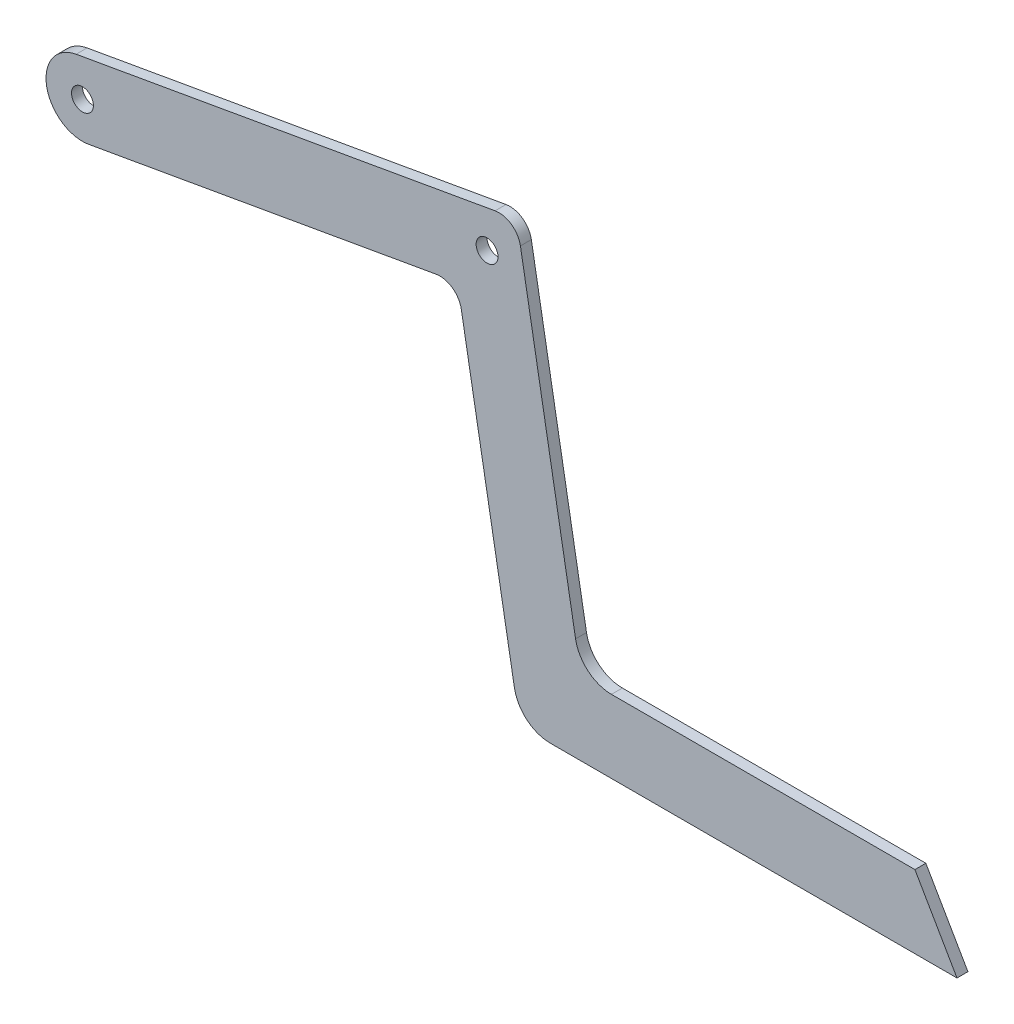
SolidWorks part; units mm, degrees
ref_plane "Front Plane" through (0, 0, 0) normal (0, 0, 1) x (1, 0, 0)
ref_plane "Top Plane" through (0, 0, 0) normal (0, 1, 0) x (1, 0, 0)
ref_plane "Right Plane" through (0, 0, 0) normal (1, 0, 0) x (0, 0, -1)
sketch "Sketch1" plane through (0, 0, 0) normal (0, 0, 1) x (1, 0, 0)
  line L0 (4.1955, 0) -> (60, 0)
  line L5 (60, 0) -> (54.2265, 10)
  line L6 (54.2265, 10) -> (12.5865, 10)
  line L8 (7.6625, 14.1318) -> (0.0956, 57.0456)
  line L9 (-60, 44.4182) -> (30.0016, 60.288) construction
  line L10 (-3.3798, 59.4791) -> (-60.8682, 49.3423)
  line L11 (-11.4914, 47.8945) -> (-59.1318, 39.4942)
  line L12 (-8.016, 45.461) -> (-0.7285, 4.1318)
  line L13 (-1.1381, 58.9821) -> (-7.8242, 49.4334) construction
  arc A3 (-0.7285, 4.1318) -> (4.1955, 0) centre (4.1955, 5) ccw
  arc A4 (7.6625, 14.1318) -> (12.5865, 10) centre (12.5865, 15) ccw
  arc A5 (0.0956, 57.0456) -> (-3.3798, 59.4791) centre (-2.8588, 56.5246) ccw
  arc A6 (-11.4914, 47.8945) -> (-8.016, 45.461) centre (-10.9704, 44.9401) cw
  arc A7 (-60.8682, 49.3423) -> (-59.1318, 39.4942) centre (-60, 44.4182) ccw
  circle A8 centre (-60, 44.4182) radius 1.5
  circle A9 centre (-4.4812, 54.2077) radius 1.5
  point P6 (0, 0)
  point P12 (8.391, 10)
  point P18 (-0.4254, 60)
  point P29 (-9.2969, 58.4357)
  dimension "D4" = 60
  dimension "D5" = 5
  dimension "D7" = 10
  dimension "D10" = 3
  dimension "D13" = 3
  dimension "D16" = 5
  dimension "D17" = 3
  dimension "D1" = 50
  dimension "D2" = 60
  dimension "D3" = 10
  dimension "D6" = 90
  dimension "D8" = 100
  dimension "D9" = 10
  dimension "D11" = 120
  dimension "D12" = 5
  dimension "D14" = 60
  dimension "D15" = 44.4182
  dimension "D18" = 5
  dimension "D19" = 5
extrude "Boss-Extrude1" add sketch "Sketch1" along normal mid plane 1.5
